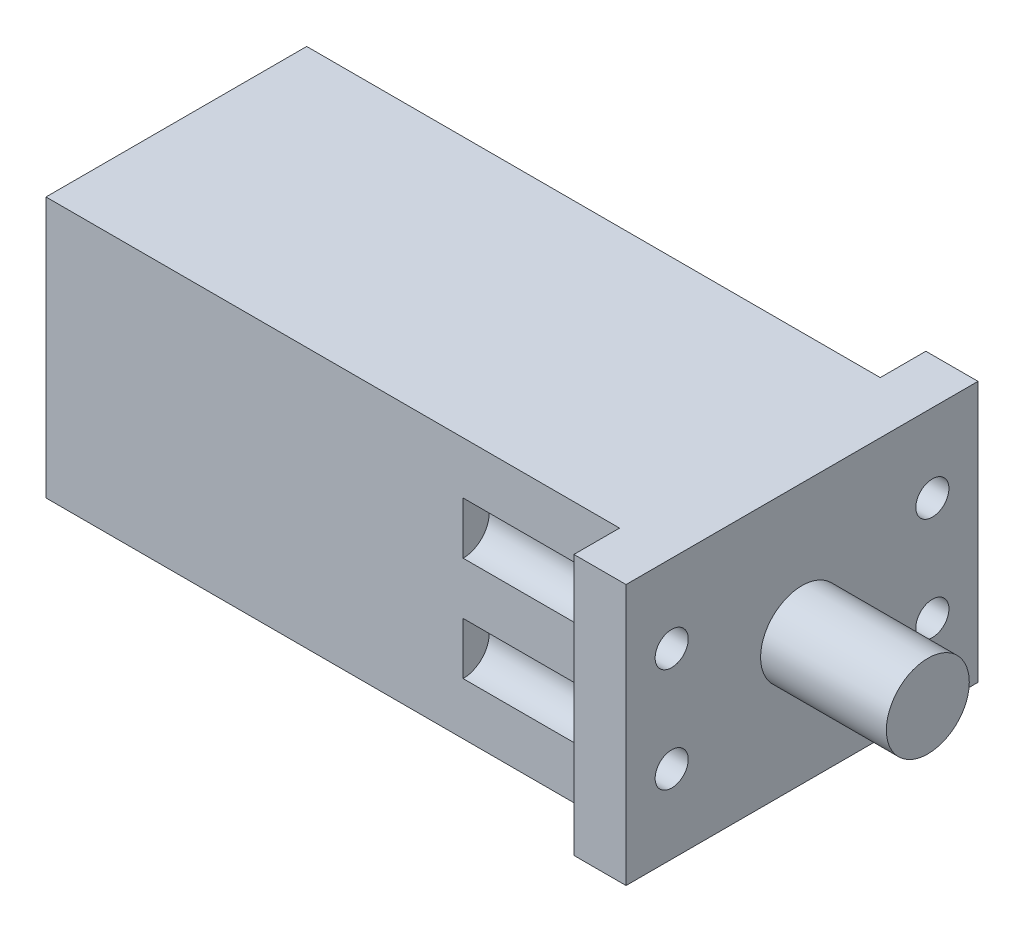
SolidWorks part; units mm, degrees
ref_plane "Front Plane" through (0, 0, 0) normal (0, 0, 1) x (1, 0, 0)
ref_plane "Top Plane" through (0, 0, 0) normal (0, 1, 0) x (1, 0, 0)
ref_plane "Right Plane" through (0, 0, 0) normal (1, 0, 0) x (0, 0, -1)
sketch "Sketch1" plane through (0, 0, 0) normal (1, 0, 0) x (0, 0, -1)
  line L1 (0, 0) -> (100, 0)
  line L2 (0, 0) -> (0, 100)
  line L3 (0, 100) -> (100, 100)
  line L4 (100, 0) -> (100, 100)
  dimension "D1" = 100
  dimension "D2" = 100
extrude "Boss-Extrude1" add sketch "Sketch1" along normal blind 240
sketch "Sketch3" plane through (0, 0, 0) normal (0, 0, 1) x (1, 0, 0)
  line L0 (240, 100) -> (0, 100) construction
  line L1 (240, 0) -> (220, 0)
  line L2 (240, 0) -> (240, 100)
  line L3 (240, 100) -> (220, 100)
  line L4 (220, 0) -> (220, 100)
  dimension "D1" = 20
extrude "Boss-Extrude2" add sketch "Sketch3" along normal blind 17.5
sketch "Sketch4" plane through (0, 0, -100) normal (0, 0, -1) x (-1, 0, 0)
  line L0 (-240, 100) -> (0, 100) construction
  line L1 (-240, 0) -> (-220, 0)
  line L2 (-240, 0) -> (-240, 100)
  line L3 (-240, 100) -> (-220, 100)
  line L4 (-220, 0) -> (-220, 100)
  dimension "D1" = 20
extrude "Boss-Extrude3" add sketch "Sketch4" along normal blind 17.5
sketch "Sketch6" plane through (240, 0, 0) normal (1, 0, 0) x (0, 0, -1)
  line L1 (-17.5, 100) -> (50, 100)
  line L2 (-17.5, 100) -> (-17.5, 50)
  line L3 (-17.5, 50) -> (50, 50)
  line L4 (50, 100) -> (50, 50)
  circle A0 centre (50, 50) radius 15.9
  dimension "D1" = 50
  dimension "D2" = 67.5
extrude "Boss-Extrude4" add sketch "Sketch6" along normal blind 48.26 contours L3 A0 L4 | L4 A0 L3
sketch "Sketch7" plane through (240, 0, 0) normal (1, 0, 0) x (0, 0, -1)
  line L1 (0, 70) -> (100, 70)
  line L2 (0, 70) -> (0, 30)
  line L3 (0, 30) -> (100, 30)
  line L4 (100, 70) -> (100, 30)
  line L5 (0, 70) -> (100, 30) construction
  line L6 (0, 30) -> (100, 70) construction
  circle A0 centre (0, 70) radius 6.35
  circle A1 centre (0, 30) radius 6.35
  circle A2 centre (100, 70) radius 6.35
  circle A3 centre (100, 30) radius 6.35
  point P0 (50, 50)
  dimension "D1" = 100
  dimension "D2" = 40
extrude "Cut-Extrude1" cut sketch "Sketch7" against normal blind 20 contours L1 A0 L2 | L2 A0 L1 | L2 A1 L3 | L3 A1 L2 | L3 A3 L4 | L4 A3 L3 | L4 A2 L1 | L1 A2 L4
sketch "Sketch8" plane through (220, 0, 0) normal (-1, 0, 0) x (0, 0, 1)
  line L0 (0, 76.35) -> (0, 63.65) construction
  line L1 (-100, 63.65) -> (-100, 76.35) construction
  circle A0 centre (0, 70) radius 10
  circle A1 centre (0, 30) radius 10
  circle A2 centre (-100, 70) radius 10
  circle A3 centre (-100, 30) radius 10
extrude "Cut-Extrude2" cut sketch "Sketch8" along normal blind 60
